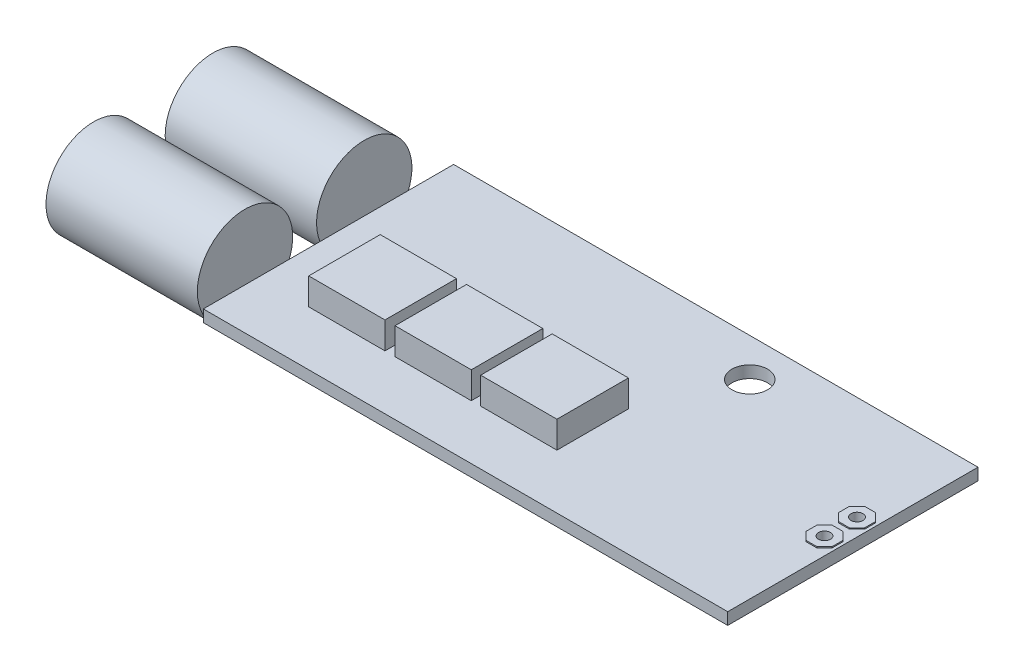
SolidWorks part; units mm, degrees
material "Стеклотекстолит СТЕФ-1"
ref_plane "Спереди" through (0, 0, 0) normal (0, 0, 1) x (1, 0, 0)
ref_plane "Сверху" through (0, 0, 0) normal (0, 1, 0) x (1, 0, 0)
ref_plane "Справа" through (0, 0, 0) normal (1, 0, 0) x (0, 0, -1)
sketch "Эскиз1" plane through (0, 0, 0) normal (0, 1, 0) x (1, 0, 0)
  line L1 (0, 0) -> (44, 0)
  line L2 (0, 0) -> (0, -21)
  line L3 (0, -21) -> (44, -21)
  line L4 (44, 0) -> (44, -21)
extrude "Бобышка-Вытянуть1" add sketch "Эскиз1" along normal blind 1
sketch "Эскиз4" plane through (0, 1, 0) normal (0, 1, 0) x (1, 0, 0)
  line L0 (42.1944, -7.7) -> (41.55, -7.7) construction
  line L1 (41.55, -7.7) -> (41.55, -8.3444) construction
  line L2 (43.75, -8.3444) -> (43.1056, -7.7)
  line L3 (43.1056, -7.7) -> (42.1944, -7.7)
  line L4 (42.1944, -7.7) -> (41.55, -8.3444)
  line L5 (41.55, -8.3444) -> (41.55, -9.2556)
  line L6 (41.55, -9.2556) -> (42.1944, -9.9)
  line L7 (42.1944, -9.9) -> (43.1056, -9.9)
  line L8 (43.1056, -9.9) -> (43.75, -9.2556)
  line L9 (43.75, -9.2556) -> (43.75, -8.3444)
  line L11 (41.55, -11.0744) -> (41.55, -11.9856)
  line L12 (42.1944, -12.63) -> (43.1056, -12.63)
  line L13 (43.1056, -12.63) -> (43.75, -11.9856)
  line L14 (41.55, -11.9856) -> (42.1944, -12.63)
  line L15 (42.1944, -10.43) -> (41.55, -11.0744)
  line L16 (43.75, -11.0744) -> (43.1056, -10.43)
  line L17 (43.1056, -10.43) -> (42.1944, -10.43)
  line L18 (43.75, -11.9856) -> (43.75, -11.0744)
  circle A0 centre (42.65, -8.8) radius 1.1 construction
  circle A1 centre (42.65, -11.53) radius 1.1 construction
  dimension "D1" = 7.7
  dimension "D2" = 2.45
extrude "Бобышка-Вытянуть3" add sketch "Эскиз4" along normal blind 0.1
sketch "Эскиз2" plane through (0, 1, 0) normal (0, 1, 0) x (1, 0, 0)
  line L0 (42.1944, -7.7) -> (43.1056, -9.9) construction
  line L1 (42.1944, -9.9) -> (43.1056, -7.7) construction
  line L2 (42.1944, -10.43) -> (43.1056, -12.63) construction
  line L3 (43.1056, -10.43) -> (42.1944, -12.63) construction
  line L4 (42.1944, -12.63) -> (43.1056, -12.63) construction
  line L5 (41.55, -11.9856) -> (42.1944, -12.63) construction
  circle A0 centre (28.05, -3.2) radius 1.5
  circle A1 centre (42.65, -8.8) radius 0.5
  circle A2 centre (42.65, -11.53) radius 0.5
  dimension "D1" = 28.05
  dimension "D2" = 3.2
extrude "Вырез-Вытянуть1" cut sketch "Эскиз2" against normal blind 1 and the other way blind 1
sketch "Эскиз3" plane through (0, 1, 0) normal (0, 1, 0) x (1, 0, 0)
  point P0 (4.271, -10.429)
  point P1 (11.514, -10.429)
  point P2 (18.7, -10.429)
  line B0 (4.271, -10.429) -> (10.671, -10.429)
  line B1 (4.271, -10.429) -> (4.271, -16.429)
  line B2 (4.271, -16.429) -> (10.671, -16.429)
  line B3 (10.671, -10.429) -> (10.671, -16.429)
  line B4 (11.514, -10.429) -> (17.914, -10.429)
  line B5 (11.514, -10.429) -> (11.514, -16.429)
  line B6 (11.514, -16.429) -> (17.914, -16.429)
  line B7 (17.914, -10.429) -> (17.914, -16.429)
  line B8 (18.7, -10.429) -> (25.1, -10.429)
  line B9 (18.7, -10.429) -> (18.7, -16.429)
  line B10 (18.7, -16.429) -> (25.1, -16.429)
  line B11 (25.1, -10.429) -> (25.1, -16.429)
  dimension "D1" = 20.829
  dimension "D2" = 6
sketch_block_instance "Блок1-1"
sketch_block "Блок1"
sketch_block_instance "Блок1-2"
sketch_block_instance "Блок1-3"
extrude "Бобышка-Вытянуть2" add sketch "Эскиз3" along normal blind 2.25 and the other way blind 3.25
sketch "Эскиз5" plane through (0, 0, 0) normal (-1, 0, 0) x (0, 0, 1)
  line L0 (0, 0) -> (21, 1) construction
  line L1 (0, 1) -> (21, 0) construction
  line L2 (5.5, 0.5) -> (15.5, 0.5) construction
  circle A0 centre (5.5, 0.5) radius 4
  circle A1 centre (15.5, 0.5) radius 4
extrude "Бобышка-Вытянуть4" add sketch "Эскиз5" along normal blind 12.7 from offset 2 separate body
